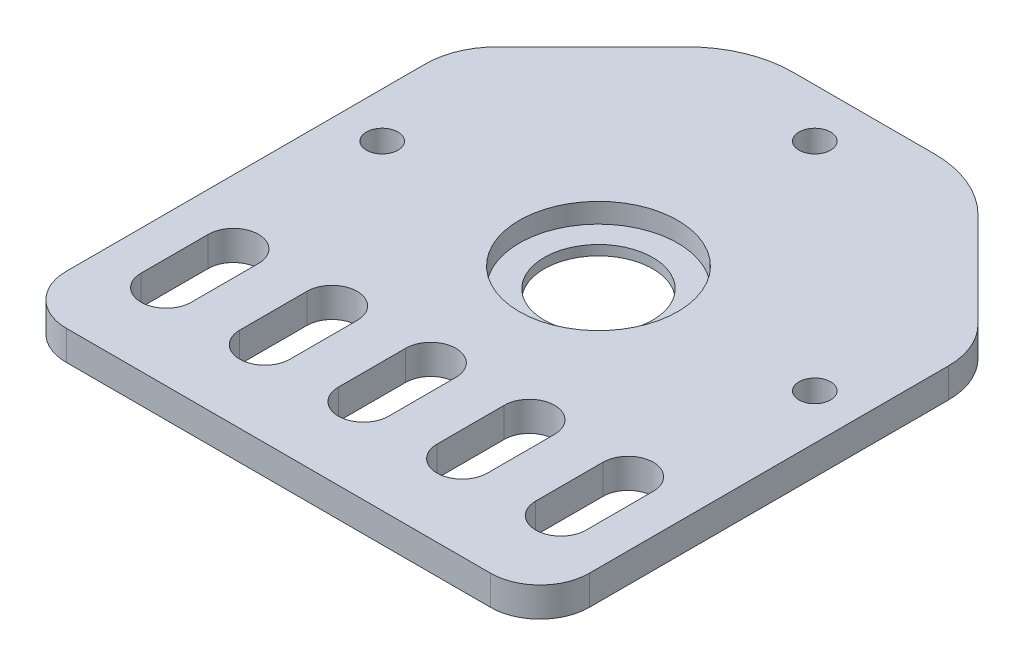
SolidWorks part; units mm, degrees
material "6061-T6 (SS)"
ref_plane "Front Plane" through (0, 0, 0) normal (0, 0, 1) x (1, 0, 0)
ref_plane "Top Plane" through (0, 0, 0) normal (0, 1, 0) x (1, 0, 0)
ref_plane "Right Plane" through (0, 0, 0) normal (1, 0, 0) x (0, 0, -1)
sketch "Sketch1" plane through (0, 0, 0) normal (0, 1, 0) x (1, 0, 0)
  line L0 (0, 0) -> (21.9203, 0) construction
  line L1 (21.5, -32.43) -> (-21.5, -32.43)
  line L2 (26.5, -27.43) -> (26.5, 8.957)
  line L3 (7.1762, 26.86) -> (-7.1762, 26.86)
  line L4 (-26.5, -27.43) -> (-26.5, 8.957)
  line L5 (0, 21.9203) -> (0, 0) construction
  line L6 (-24.3765, 14.0835) -> (-14.7281, 23.7319)
  line L7 (24.3765, 14.0835) -> (14.7281, 23.7319)
  line L8 (20, -23.81) -> (20, -17) construction
  line L9 (17.45, -23.81) -> (17.45, -17)
  line L10 (22.55, -23.81) -> (22.55, -17)
  line L11 (10, -23.81) -> (10, -17) construction
  line L12 (7.45, -23.81) -> (7.45, -17)
  line L13 (12.55, -23.81) -> (12.55, -17)
  line L14 (0, -23.81) -> (0, -17) construction
  line L15 (-2.55, -23.81) -> (-2.55, -17)
  line L16 (2.55, -23.81) -> (2.55, -17)
  line L17 (-10, -23.81) -> (-10, -17) construction
  line L18 (-12.55, -23.81) -> (-12.55, -17)
  line L19 (-7.45, -23.81) -> (-7.45, -17)
  line L20 (-20, -23.81) -> (-20, -17) construction
  line L21 (-22.55, -23.81) -> (-22.55, -17)
  line L22 (-17.45, -23.81) -> (-17.45, -17)
  line L23 (20, -23.81) -> (10, -23.81) construction
  arc A0 (-21.5, -32.43) -> (-26.5, -27.43) centre (-21.5, -27.43) cw
  arc A1 (21.5, -32.43) -> (26.5, -27.43) centre (21.5, -27.43) ccw
  circle A2 centre (21.9203, 0) radius 1.6
  circle A3 centre (-21.9203, 0) radius 1.6
  circle A4 centre (0, 0) radius 5.5
  circle A5 centre (0, 21.9203) radius 1.6
  arc A6 (17.45, -23.81) -> (22.55, -23.81) centre (20, -23.81) ccw
  arc A7 (22.55, -17) -> (17.45, -17) centre (20, -17) ccw
  arc A8 (7.45, -23.81) -> (12.55, -23.81) centre (10, -23.81) ccw
  arc A9 (12.55, -17) -> (7.45, -17) centre (10, -17) ccw
  arc A10 (-2.55, -23.81) -> (2.55, -23.81) centre (0, -23.81) ccw
  arc A11 (2.55, -17) -> (-2.55, -17) centre (0, -17) ccw
  arc A12 (-12.55, -23.81) -> (-7.45, -23.81) centre (-10, -23.81) ccw
  arc A13 (-7.45, -17) -> (-12.55, -17) centre (-10, -17) ccw
  arc A14 (-22.55, -23.81) -> (-17.45, -23.81) centre (-20, -23.81) ccw
  arc A15 (-17.45, -17) -> (-22.55, -17) centre (-20, -17) ccw
  arc A16 (-24.3765, 14.0835) -> (-26.5, 8.957) centre (-19.25, 8.957) ccw
  arc A17 (24.3765, 14.0835) -> (26.5, 8.957) centre (19.25, 8.957) cw
  arc A18 (-14.7281, 23.7319) -> (-7.1762, 26.86) centre (-7.1762, 16.18) cw
  arc A19 (7.1762, 26.86) -> (14.7281, 23.7319) centre (7.1762, 16.18) cw
  point P21 (20, -20.405)
  point P29 (10, -20.405)
  point P36 (0, -20.405)
  point P43 (-10, -20.405)
  point P50 (-20, -20.405)
  point P58 (-26.5, 11.96)
  point P61 (26.5, 11.96)
  point P64 (-11.6, 26.86)
  point P67 (11.6, 26.86)
  dimension "D2" = 5
  dimension "D3" = 32.43
  dimension "D5" = 45
  dimension "D7" = 31
  dimension "D10" = 5.1
  dimension "D4" = 11
  dimension "D8" = 3.2
  dimension "D14" = 5
  dimension "D15" = 7.25
  dimension "D6" = 23.2
  dimension "D16" = 10.68
  dimension "D1" = 59.29
  dimension "D9" = 53
  dimension "D11" = 6.81
  dimension "D12" = 8.62
  dimension "D13" = 10
extrude "Boss-Extrude1" add sketch "Sketch1" along normal blind 3
sketch "Sketch2" plane through (0, 3, 0) normal (0, 1, 0) x (1, 0, 0)
  circle A0 centre (0, 0) radius 8.025
  dimension "D1" = 16.05
extrude "Cut-Extrude1" cut sketch "Sketch2" against normal blind 2
